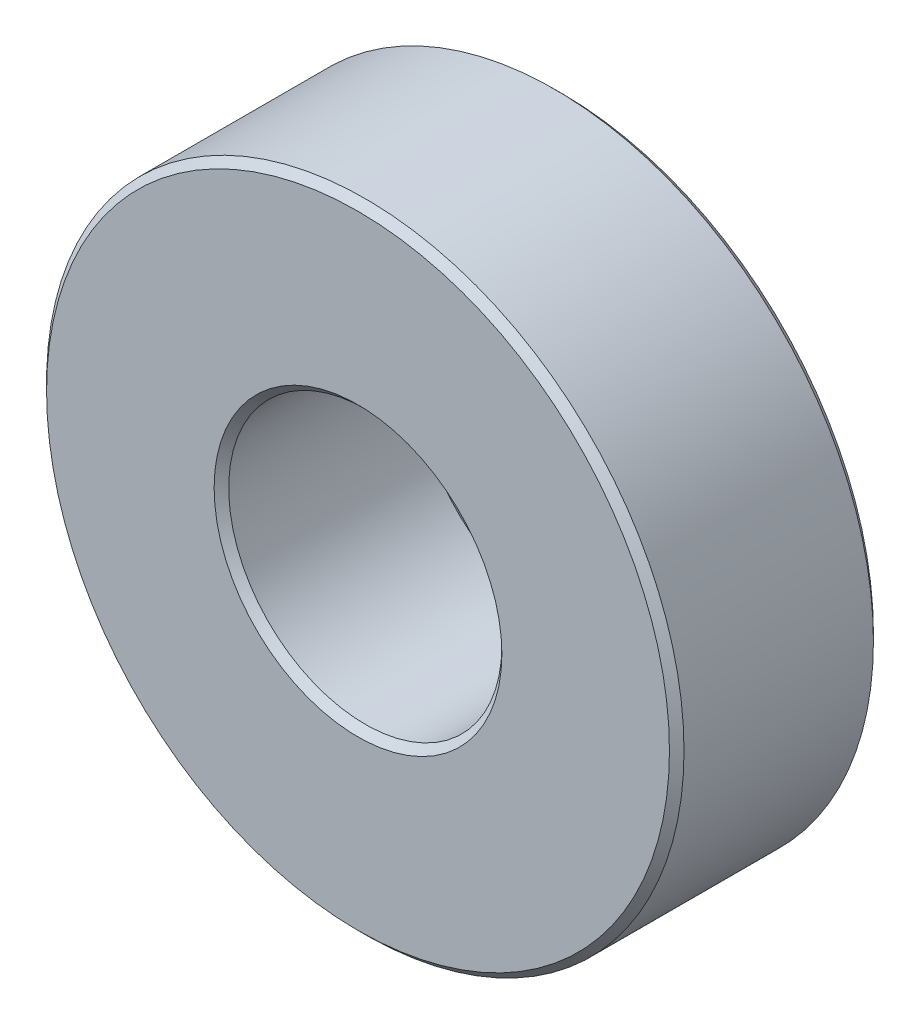
SolidWorks part; units mm, degrees
material "PVC Rigid"
ref_plane "Front Plane" through (0, 0, 0) normal (0, 0, 1) x (1, 0, 0)
ref_plane "Top Plane" through (0, 0, 0) normal (0, 1, 0) x (1, 0, 0)
ref_plane "Right Plane" through (0, 0, 0) normal (1, 0, 0) x (0, 0, -1)
sketch "Sketch1" plane through (0, 0, 0) normal (0, 1, 0) x (1, 0, 0)
  line L1 (4.7625, 0) -> (4.7625, -7.112)
  line L3 (4.7625, -7.112) -> (11.1125, -7.112)
  line L5 (11.1125, -7.112) -> (11.1125, 0)
  line L7 (11.1125, 0) -> (4.7625, 0)
  line L8 (0, 0) -> (0, -7.112) construction
  dimension "D1" = 7.112
  dimension "D2" = 6.35
  dimension "D3" = 9.525
revolve "Revolve1" add sketch "Sketch1" angle 360 about L8
chamfer "Chamfer1" distance 0.254 angle 45 4 edges at (11.1125, 0, 0) (4.7625, 0, 0) (4.7625, 0, 7.112) (11.1125, 0, 7.112)
